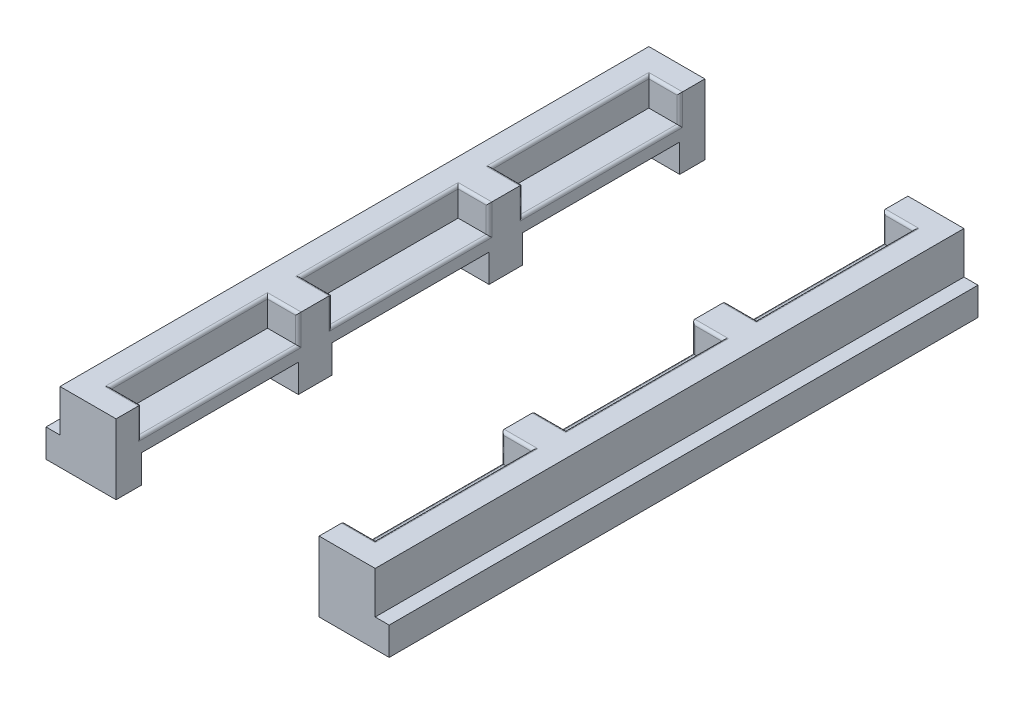
SolidWorks part; units mm, degrees
ref_plane "Ebene vorne" through (0, 0, 0) normal (0, 0, 1) x (1, 0, 0)
ref_plane "Ebene oben" through (0, 0, 0) normal (0, 1, 0) x (1, 0, 0)
ref_plane "Ebene rechts" through (0, 0, 0) normal (1, 0, 0) x (0, 0, -1)
sketch "Skizze1" plane through (0, 0, 0) normal (0, 1, 0) x (1, 0, 0)
  line L1 (-70, -105) -> (70, -105)
  line L2 (-70, -105) -> (-70, 105)
  line L3 (-70, 105) -> (70, 105)
  line L4 (70, -105) -> (70, 105)
  line L5 (-70, -105) -> (70, 105) construction
  line L6 (-70, 105) -> (70, -105) construction
  point P0 (0, 0)
  dimension "D1" = 210
  dimension "D2" = 140
extrude "Aufsatz-Linear austragen1" add sketch "Skizze1" along normal blind 2
sketch "Skizze2" plane through (0, 2, 0) normal (0, 1, 0) x (1, 0, 0)
  line L0 (0, 105) -> (0, -105) construction
  line L1 (-46.2, -27) -> (46.2, -27) construction
  line L2 (-46.2, -27) -> (-46.2, 27) construction
  line L3 (-46.2, 27) -> (46.2, 27) construction
  line L4 (46.2, -27) -> (46.2, 27) construction
  line L5 (-46.2, -27) -> (46.2, 27) construction
  line L6 (-46.2, 27) -> (46.2, -27) construction
  line L7 (70, 105) -> (-70, 105) construction
  line L8 (-70, -105) -> (70, -105) construction
  line L9 (-45.4738, -92.1512) -> (45.4738, -92.1512) construction
  line L10 (-46.2, 39) -> (46.2, 39) construction
  line L11 (-46.2, 39) -> (-46.2, 93) construction
  line L12 (-46.2, 93) -> (46.2, 93) construction
  line L13 (46.2, 39) -> (46.2, 93) construction
  line L14 (-46.2, 39) -> (46.2, 93) construction
  line L15 (-46.2, 93) -> (46.2, 39) construction
  line L16 (-45.4738, -92.1512) -> (-45.4738, -39) construction
  line L17 (-45.4738, -39) -> (45.4738, -39) construction
  line L18 (45.4738, -92.1512) -> (45.4738, -39) construction
  line L19 (-45.4738, -92.1512) -> (45.4738, -39) construction
  line L20 (-45.4738, -39) -> (45.4738, -92.1512) construction
  line L22 (-56.2, -105) -> (-36.2, -105)
  line L23 (-56.2, -105) -> (-56.2, 105)
  line L24 (-56.2, 105) -> (-36.2, 105)
  line L25 (-36.2, -105) -> (-36.2, 105)
  line L26 (-56.2, -105) -> (-36.2, 105) construction
  line L27 (-56.2, 105) -> (-36.2, -105) construction
  line L28 (36.2, -105) -> (56.2, -105)
  line L29 (36.2, -105) -> (36.2, 105)
  line L30 (36.2, 105) -> (56.2, 105)
  line L31 (56.2, -105) -> (56.2, 105)
  line L32 (36.2, -105) -> (56.2, 105) construction
  line L33 (36.2, 105) -> (56.2, -105) construction
  point P0 (0, 0)
  point P12 (0, 66)
  point P17 (0, -65.5756)
  point P19 (-46.2, 0)
  point P27 (46.2, 0)
  dimension "D1" = 54
  dimension "D2" = 92.4
  dimension "D3" = 54
  dimension "D4" = 92.4
  dimension "D5" = 12
  dimension "D6" = 12
  dimension "D7" = 20
extrude "Aufsatz-Linear austragen2" add sketch "Skizze2" along normal blind 15
sketch "Skizze3" plane through (0, 17, 0) normal (0, 1, 0) x (1, 0, 0)
  line L0 (0, 105) -> (0, -105) construction
  line L1 (-47.2, -28) -> (47.2, -28)
  line L2 (-47.2, -28) -> (-47.2, 28)
  line L3 (-47.2, 28) -> (47.2, 28)
  line L4 (47.2, -28) -> (47.2, 28)
  line L5 (-47.2, -28) -> (47.2, 28) construction
  line L6 (-47.2, 28) -> (47.2, -28) construction
  line L7 (36.2, 105) -> (-36.2, 105) construction
  line L8 (-36.2, -105) -> (36.2, -105) construction
  line L9 (-47.2, -96) -> (47.2, -96)
  line L10 (-47.2, 40) -> (47.2, 40)
  line L11 (-47.2, 40) -> (-47.2, 96)
  line L12 (-47.2, 96) -> (47.2, 96)
  line L13 (47.2, 40) -> (47.2, 96)
  line L14 (-47.2, 40) -> (47.2, 96) construction
  line L15 (-47.2, 96) -> (47.2, 40) construction
  line L16 (-47.2, -96) -> (-47.2, -40)
  line L17 (-47.2, -40) -> (47.2, -40)
  line L18 (47.2, -96) -> (47.2, -40)
  line L19 (-47.2, -96) -> (47.2, -40) construction
  line L20 (-47.2, -40) -> (47.2, -96) construction
  point P0 (0, 0)
  point P12 (0, 68)
  point P17 (0, -68)
  dimension "D1" = 56
  dimension "D2" = 94.4
  dimension "D5" = 12
  dimension "D6" = 12
extrude "Schnitt-Linear austragen1" cut sketch "Skizze3" against normal blind 10
fillet "Verrundung1" radius 1 36 edges at (36.2, 7, -68) (36.2, 7, 0) (36.2, 7, 68) (36.2, 12, 96) (36.2, 12, 40) (36.2, 12, 28) (36.2, 12, -28) (36.2, 12, -40) (36.2, 12, -96) (41.7, 17, -96) (41.7, 17, -40) (41.7, 17, 28) (41.7, 17, -28) (41.7, 17, 96) (41.7, 17, 40) (47.2, 17, 68) (47.2, 17, 0) (47.2, 17, -68) (-36.2, 7, 0) (-36.2, 7, -68) (-36.2, 7, 68) (-36.2, 12, 96) (-36.2, 12, 40) (-36.2, 12, 28) (-36.2, 12, -28) (-36.2, 12, -40) (-36.2, 12, -96) (-41.7, 17, -96) (-47.2, 17, -68) (-41.7, 17, -40) (-41.7, 17, -28) (-47.2, 17, 0) (-41.7, 17, 28) (-41.7, 17, 96) (-47.2, 17, 68) (-41.7, 17, 40)
sketch "Skizze4" plane through (0, 0, 0) normal (0, -1, 0) x (1, 0, 0)
  line L1 (-70, -105) -> (70, -105)
  line L2 (-70, -105) -> (-70, 105)
  line L3 (-70, 105) -> (70, 105)
  line L4 (70, -105) -> (70, 105)
  line L5 (-70, -105) -> (70, 105) construction
  line L6 (-70, 105) -> (70, -105) construction
  point P0 (0, 0)
extrude "Schnitt-Linear austragen2" cut sketch "Skizze4" against normal blind 2
sketch "Skizze7" plane through (0, 2, 0) normal (0, -1, 0) x (1, 0, 0)
  line L0 (-36.2, 105) -> (-36.2, -105) construction
  line L1 (-36.2, 105) -> (-61.2, 105)
  line L2 (-36.2, 105) -> (-36.2, -105)
  line L3 (-36.2, -105) -> (-61.2, -105)
  line L4 (-61.2, 105) -> (-61.2, -105)
  line L6 (36.2, 105) -> (61.2, 105)
  line L7 (36.2, 105) -> (36.2, -105)
  line L8 (36.2, -105) -> (61.2, -105)
  line L9 (61.2, 105) -> (61.2, -105)
  point P4 (0, 0)
  dimension "D1" = 25
extrude "Aufsatz-Linear austragen3" add sketch "Skizze7" along normal blind 10
sketch "Skizze5" plane through (0, -8, 0) normal (0, -1, 0) x (1, 0, 0)
  line L0 (0, 107.3569) -> (0, -122.9597) construction
  line L1 (-55.2, -28) -> (55.2, -28)
  line L2 (-55.2, -28) -> (-55.2, 28)
  line L3 (-55.2, 28) -> (55.2, 28)
  line L4 (55.2, -28) -> (55.2, 28)
  line L5 (-55.2, -28) -> (55.2, 28) construction
  line L6 (-55.2, 28) -> (55.2, -28) construction
  line L7 (-55.2, -96) -> (55.2, -96)
  line L8 (-55.2, -96) -> (-55.2, -40)
  line L9 (-55.2, -40) -> (55.2, -40)
  line L10 (55.2, -96) -> (55.2, -40)
  line L11 (-55.2, -96) -> (55.2, -40) construction
  line L12 (-55.2, -40) -> (55.2, -96) construction
  line L13 (-55.2, 40) -> (55.2, 40)
  line L14 (-55.2, 40) -> (-55.2, 96)
  line L15 (-55.2, 96) -> (55.2, 96)
  line L16 (55.2, 40) -> (55.2, 96)
  line L17 (-55.2, 40) -> (55.2, 96) construction
  line L18 (-55.2, 96) -> (55.2, 40) construction
  point P0 (0, 0)
  point P8 (0, -68)
  point P13 (0, -76.1512)
  point P14 (0, 68)
  point P19 (0, 0)
  point P20 (0, 0)
  point P21 (0, 70.3292)
  dimension "D1" = 110.4
  dimension "D2" = 56
  dimension "D3" = 12
  dimension "D4" = 12
extrude "Schnitt-Linear austragen3" cut sketch "Skizze5" against normal blind 10
